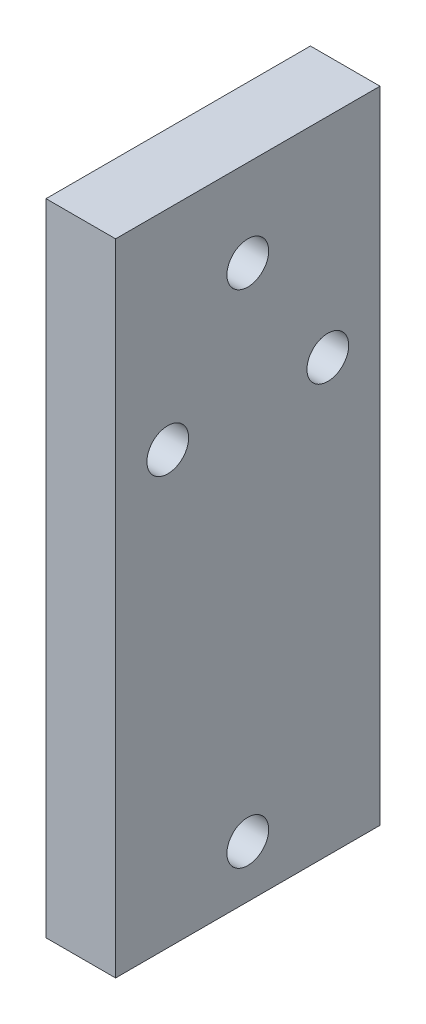
SolidWorks part; units mm, degrees
ref_plane "Front Plane" through (0, 0, 0) normal (0, 0, 1) x (1, 0, 0)
ref_plane "Top Plane" through (0, 0, 0) normal (0, 1, 0) x (1, 0, 0)
ref_plane "Right Plane" through (0, 0, 0) normal (1, 0, 0) x (0, 0, -1)
sketch "Sketch1" plane through (0, 0, 0) normal (1, 0, 0) x (0, 0, -1)
  line L1 (-17.6562, 8.3438) -> (20.3438, 8.3438)
  line L2 (-17.6562, 8.3438) -> (-17.6562, -83.6562)
  line L3 (-17.6562, -83.6562) -> (20.3438, -83.6562)
  line L4 (20.3438, 8.3438) -> (20.3438, -83.6562)
  dimension "D1" = 38
  dimension "D2" = 92
extrude "Boss-Extrude1" add sketch "Sketch1" along normal blind 10
sketch "Sketch4" plane through (0, 0, 0) normal (-1, 0, 0) x (0, 0, 1)
  line L1 (2.1562, -0.6562) -> (-4.8438, -0.6562)
  line L2 (2.1562, -0.6562) -> (2.1562, -7.6562)
  line L3 (2.1562, -7.6562) -> (-4.8438, -7.6562)
  line L4 (-4.8438, -0.6562) -> (-4.8438, -7.6562)
  line L5 (-20.3438, -83.6562) -> (-20.3438, 8.3438) construction
  line L9 (-20.3438, 8.3438) -> (17.6562, 8.3438) construction
  dimension "D1" = 7
  dimension "D2" = 7
  dimension "D3" = 15.5
  dimension "D4" = 9
extrude "Cut-Extrude3" cut sketch "Sketch4" against normal blind 3
sketch "Sketch7" plane through (3, 0, 0) normal (-1, 0, 0) x (0, 0, 1)
  line L0 (2.1562, -7.6562) -> (2.1562, -0.6562) construction
  line L1 (-4.8438, -7.6562) -> (2.1562, -7.6562) construction
  circle A0 centre (-1.3438, -4.1562) radius 3
  dimension "D1" = 6
  dimension "D3" = 3.5
  dimension "D2" = 3.5
extrude "Cut-Extrude4" cut sketch "Sketch7" against normal through all
sketch "Sketch8" plane through (0, 0, 0) normal (-1, 0, 0) x (0, 0, 1)
  circle A0 centre (-1.3437, -76.1562) radius 3
  dimension "D1" = 6
extrude "Cut-Extrude5" cut sketch "Sketch8" against normal through all
sketch "Sketch9" plane through (0, 0, 0) normal (-1, 0, 0) x (0, 0, 1)
  circle A0 centre (10.1562, -21.6562) radius 3
  circle A1 centre (-12.8438, -21.6562) radius 3
extrude "Cut-Extrude6" cut sketch "Sketch9" against normal through all
